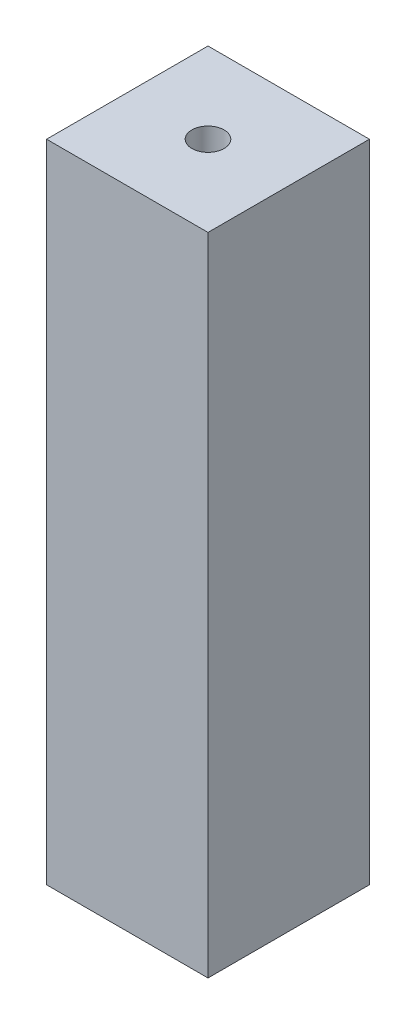
SolidWorks part; units mm, degrees
ref_plane "Front Plane" through (0, 0, 0) normal (0, 0, 1) x (1, 0, 0)
ref_plane "Top Plane" through (0, 0, 0) normal (0, 1, 0) x (1, 0, 0)
ref_plane "Right Plane" through (0, 0, 0) normal (1, 0, 0) x (0, 0, -1)
sketch "Sketch1" plane through (0, 0, 0) normal (0, 1, 0) x (1, 0, 0)
  line L0 (0, -8.25) -> (0, 8.25) construction
  line L1 (-7.5, 7.5) -> (7.5, 7.5)
  line L2 (-7.5, 7.5) -> (-7.5, -7.5)
  line L3 (-7.5, -7.5) -> (7.5, -7.5)
  line L4 (7.5, 7.5) -> (7.5, -7.5)
  line L5 (-8.25, 0) -> (8.25, 0) construction
  circle A0 centre (0, 0) radius 1.5
  dimension "D5" = 3
  dimension "D1" = 15
  dimension "D2" = 15
  dimension "D3" = 7.5
  dimension "D4" = 7.5
extrude "Boss-Extrude1" add sketch "Sketch1" along normal blind 60
